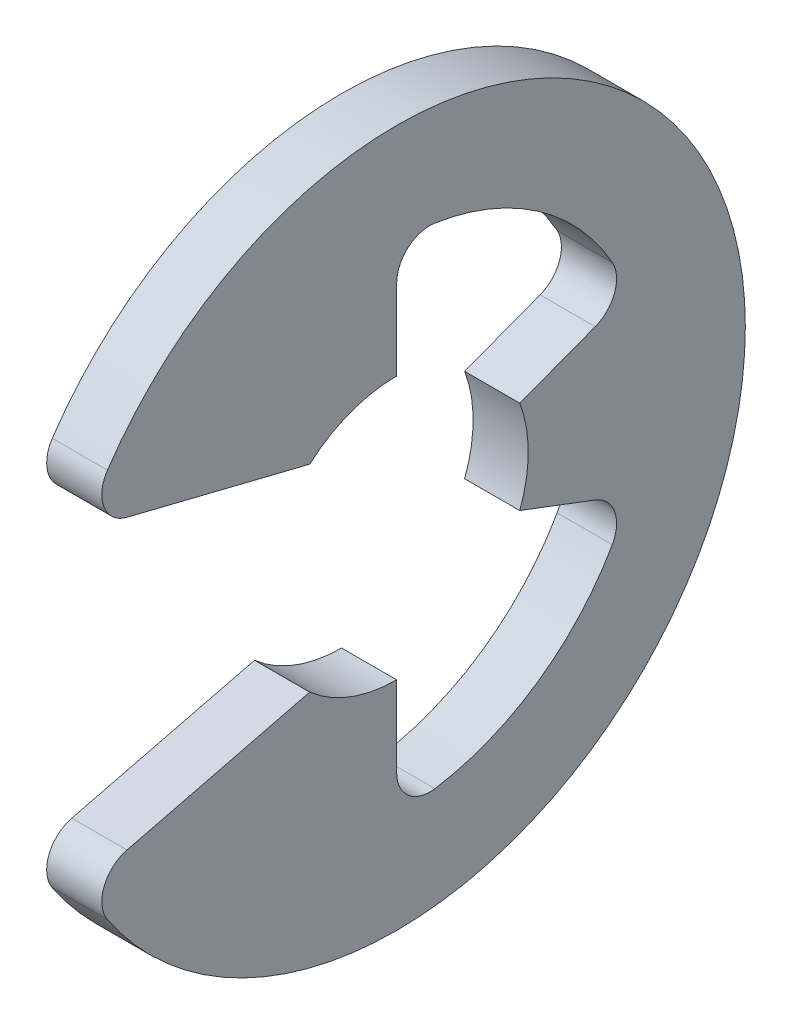
SolidWorks part; units mm, degrees
ref_plane "Plano frontal" through (0, 0, 0) normal (0, 0, 1) x (1, 0, 0)
ref_plane "Plano superior" through (0, 0, 0) normal (0, 1, 0) x (1, 0, 0)
ref_plane "Plano direito" through (0, 0, 0) normal (1, 0, 0) x (0, 0, -1)
ref_plane "Plano1" through (0.35, 0, 0) normal (1, 0, 0) x (0, 0, -1)
sketch "Esboço1" plane through (0.35, 0, 0) normal (1, 0, 0) x (0, 0, -1)
  line L0 (-1.1046, -1.2525) -> (-3.4239, -1.8283)
  line L1 (-3.4239, 1.8283) -> (-1.1046, 1.2525)
  line L2 (0, 1.67) -> (0, 2.6933)
  line L3 (2.5193, 0.9522) -> (1.5621, 0.5904)
  line L4 (1.5621, -0.5904) -> (2.5193, -0.9522)
  line L5 (0, -2.6933) -> (0, -1.67)
  arc A0 (-3.4239, -1.8283) -> (-3.6712, -2.4704) centre (-3.3227, -2.2359) ccw
  arc A1 (-3.6712, -2.4704) -> (-3.6712, 2.4704) centre (0, 0) ccw
  arc A2 (-3.6712, 2.4704) -> (-3.4239, 1.8283) centre (-3.3227, 2.2359) ccw
  arc A3 (-1.1046, 1.2525) -> (0, 1.67) centre (0, 0) cw
  arc A4 (0, 2.6933) -> (0.4847, 3.1082) centre (0.42, 2.6933) cw
  arc A5 (0.4847, 3.1082) -> (2.7361, 1.5523) centre (0, 0) cw
  arc A6 (2.7361, 1.5523) -> (2.5193, 0.9522) centre (2.3708, 1.3451) cw
  arc A7 (1.5621, 0.5904) -> (1.5621, -0.5904) centre (0, 0) cw
  arc A8 (2.5193, -0.9522) -> (2.7361, -1.5523) centre (2.3708, -1.3451) cw
  arc A9 (2.7361, -1.5523) -> (0.4847, -3.1082) centre (0, 0) cw
  arc A10 (0.4847, -3.1082) -> (0, -2.6933) centre (0.42, -2.6933) cw
  arc A11 (0, -1.67) -> (-1.1046, -1.2525) centre (0, 0) cw
extrude "Ressalto-extrusão1" add sketch "Esboço1" against normal blind 0.7
